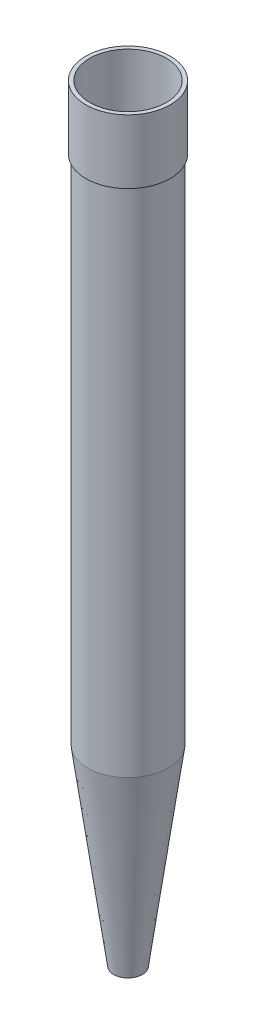
SolidWorks part; units mm, degrees
material "1100-H12 Rod (SS)"
ref_plane "Front Plane" through (0, 0, 0) normal (0, 0, 1) x (1, 0, 0)
ref_plane "Top Plane" through (0, 0, 0) normal (0, 1, 0) x (1, 0, 0)
ref_plane "Right Plane" through (0, 0, 0) normal (1, 0, 0) x (0, 0, -1)
sketch "Sketch1" plane through (0, 0, 0) normal (0, 0, 1) x (1, 0, 0)
  line L34 (0, 37.9715) -> (0, 145.1784) construction
  line L44 (19.05, 0) -> (53.34, 254)
  line L45 (53.34, 254) -> (53.34, 931.3333)
  line L49 (50.8, 1016) -> (50.8, 254)
  line L50 (50.8, 254) -> (16.51, 0)
  line L51 (16.51, 0) -> (19.05, 0)
  line L53 (55.88, 1016) -> (55.88, 931.3333)
  line L54 (55.88, 931.3333) -> (53.34, 931.3333)
  line L55 (50.8, 1016) -> (55.88, 1016)
  dimension "ScopeTaper" = 254
  dimension "SlopeStraight" = 762
  dimension "ScopeEndRing" = 84.6667
  dimension "ScopeInsideRadius" = 50.8
  dimension "ScopeEndRingThickness" = 5.08
  dimension "ScopeEyeThickness" = 2.54
  dimension "OutsideEyeRadius" = 19.05
  dimension "ScopeOutsideRadius" = 53.34
revolve "Revolve1" add sketch "Sketch1" angle 360 about L34
equation "\"ScopeLengthUnit\"= 10 * \"ScaleFactor\""
equation "\"EyepieceRadius\"= 0.75 * \"ScaleFactor\""
equation "\"ScopeThickness\"= 0.1 * \"ScaleFactor\""
equation "\"ScopeLensWidth\"= 2 * \"ScaleFactor\""
equation "\"SlopeStraight@Sketch1\"=\"ScopeLengthUnit\"*3"
equation "\"ScopeEndRing@Sketch1\"=\"ScopeLengthUnit\"/3"
equation "\"ScopeInsideRadius@Sketch1\"=\"ScopeLensWidth\""
equation "\"ScopeEndRingThickness@Sketch1\"=\"ScopeThickness\"*2"
equation "\"ScopeEyeThickness@Sketch1\"=\"ScopeThickness\""
equation "\"OutsideEyeRadius@Sketch1\"=\"EyepieceRadius\""
equation "\"ScopeOutsideRadius\"= 2.1 * \"ScaleFactor\""
equation "\"ScopeOutsideRadius@Sketch1\"=\"ScopeOutsideRadius\""
equation "\"PegWidth\"=1"
equation "\"SupportOutsideDiam\"= \"ScopeOutsideRadius\" * 2 + .25"
equation "\"RotatingDiskDiam\"=3"
equation "\"LegSeatWidth\"=4 "
equation "\"BoltCircleDiam\"= ( \"RotatingDiskDiam\" + \"RotatingDiskHousingDiameter\" ) / 2"
equation "\"RotatingDiskHousingDiameter\"= (\"RotatingDiskDiam\" + 2)"
equation "\"LegSeatHeight\"=2"
equation "\"LegThickness\"=0.25"
equation "\"LegHeight\"=48"
equation "\"LegBoltDiam\"=0.25"
equation "\"PinHeight\"=\"RotDiskLidHeight\" + \"RotDiskHeight\" + \"PinBoltDiam\"*3"
equation "\"PinBoltDiam\"=0.25"
equation "\"RotDiskHeight\"=0.5"
equation "\"RotDiskLidHeight\"= 0.5"
equation "\"DiskSeatPinDiam\"=0.25"
equation "\"ScaleFactor\"= 1"
